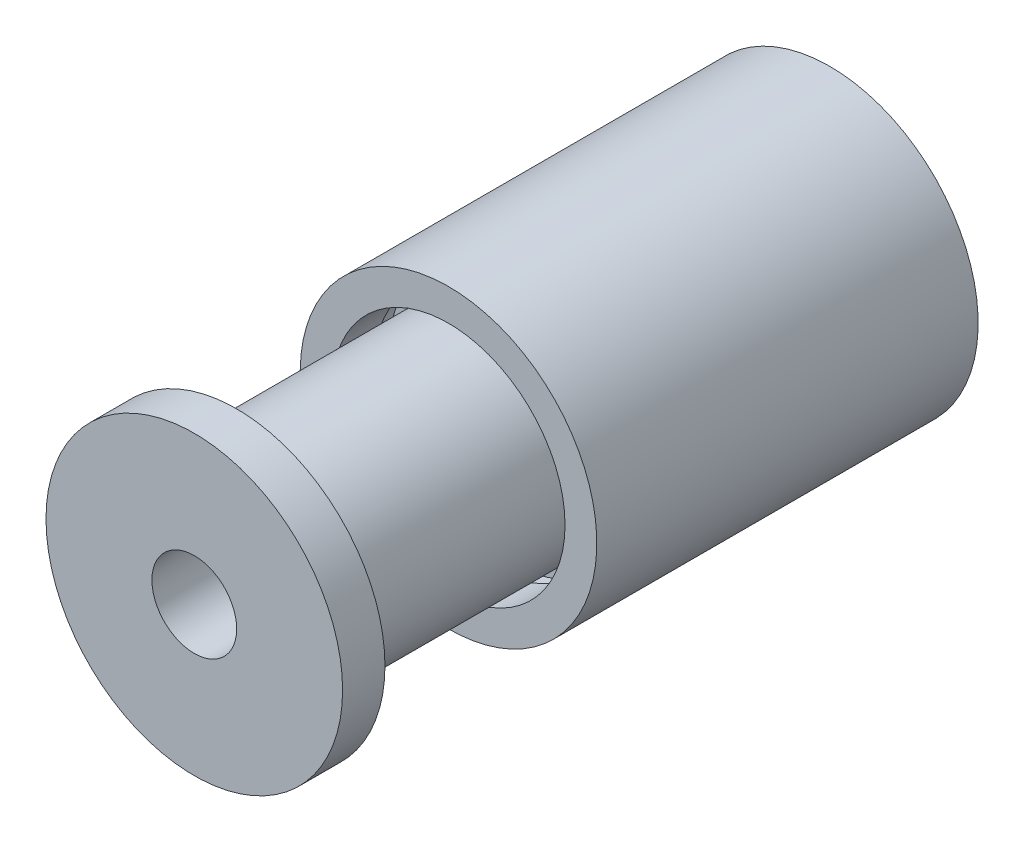
SolidWorks part; units mm, degrees
ref_plane "Alzado" through (0, 0, 0) normal (0, 0, 1) x (1, 0, 0)
ref_plane "Planta" through (0, 0, 0) normal (0, 1, 0) x (1, 0, 0)
ref_plane "Vista lateral" through (0, 0, 0) normal (1, 0, 0) x (0, 0, -1)
sketch "Croquis1" plane through (0, 0, 0) normal (0, 0, 1) x (1, 0, 0)
  circle A0 centre (0, 0) radius 25
  circle A1 centre (0, 0) radius 10
  dimension "D1" = 50
  dimension "D2" = 20
extrude "Saliente-Extruir1" add sketch "Croquis1" along normal blind 70
sketch "Croquis3" plane through (0, 0, 70) normal (0, 0, 1) x (1, 0, 0)
  circle A0 centre (0, 0) radius 35
  circle A1 centre (0, 0) radius 25
  dimension "D1" = 50
  dimension "D2" = 70
extrude "Saliente-Extruir2" add sketch "Croquis3" against normal blind 10
sketch "Croquis4" plane through (0, 0, 0) normal (0, 0, -1) x (-1, 0, 0)
  circle A0 centre (0, 0) radius 27.5
  circle A1 centre (0, 0) radius 30
  dimension "D1" = 55
  dimension "D2" = 60
extrude "Saliente-Extruir3" add sketch "Croquis4" against normal blind 10 separate body
sketch "Croquis6" plane through (0, 0, 10) normal (0, 0, 1) x (1, 0, 0)
  circle A0 centre (0, 0) radius 35 construction
  circle A1 centre (0, 0) radius 30 construction
  ellipse E0 centre (0, 0) end of major axis (-31.2241, -15.8132) minor radius 35
  ellipse E1 centre (0, 0) end of major axis (-24.8028, 16.8766) minor radius 30
extrude "Saliente-Extruir4" add sketch "Croquis6" against normal blind 90
sketch "Croquis7" plane through (0, 0, 0) normal (0, 0, -1) x (-1, 0, 0)
  circle A0 centre (0, 0) radius 25
  circle A1 centre (0, 0) radius 10
  dimension "D1" = 50
  dimension "D2" = 20
extrude "Saliente-Extruir5" add sketch "Croquis7" along normal blind 10
sketch "Croquis8" plane through (0, 0, -10) normal (0, 0, -1) x (-1, 0, 0)
  circle A0 centre (0, 0) radius 25
  circle A1 centre (0, 0) radius 29
  dimension "D1" = 58
  dimension "D2" = 50
extrude "Saliente-Extruir6" add sketch "Croquis8" against normal blind 5
